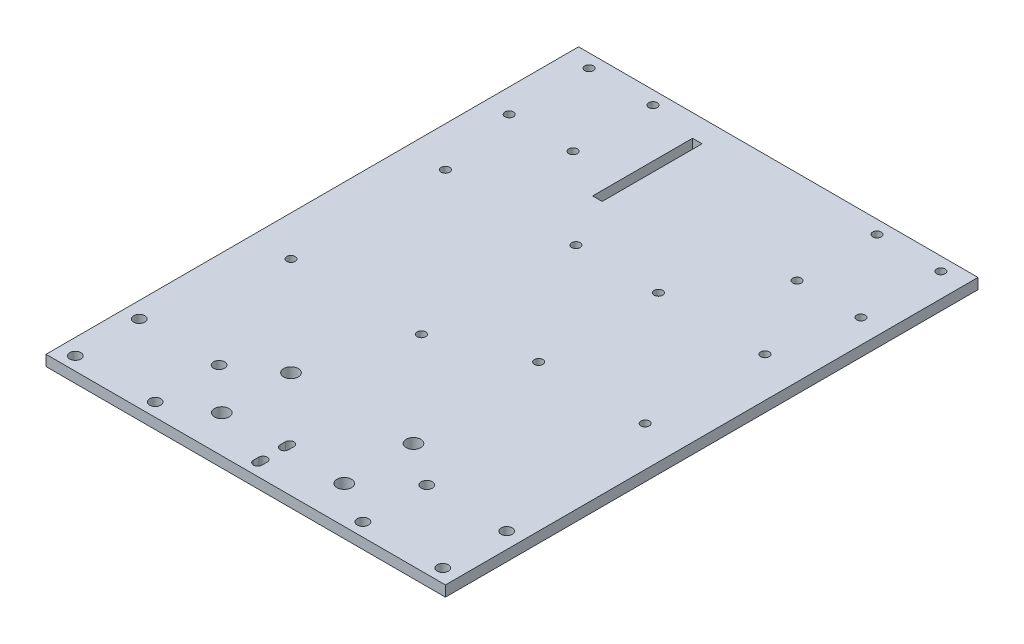
SolidWorks part; units mm, degrees
ref_plane "前视基准面" through (0, 0, 0) normal (0, 0, 1) x (1, 0, 0)
ref_plane "上视基准面" through (0, 0, 0) normal (0, 1, 0) x (1, 0, 0)
ref_plane "右视基准面" through (0, 0, 0) normal (1, 0, 0) x (0, 0, -1)
sketch "草图1" plane through (0, 0, 0) normal (0, 1, 0) x (1, 0, 0)
  line L0 (-75, 70) -> (75, 70)
  line L1 (75, -130) -> (-75, -130)
  line L2 (75, -130) -> (75, 70)
  line L4 (-75, -130) -> (-75, 70)
  point P0 (0, 0)
  dimension "D1" = 150
  dimension "D2" = 200
extrude "凸台-拉伸1" add sketch "草图1" along normal blind 4
sketch "草图2" plane through (0, 4, 0) normal (0, 1, 0) x (1, 0, 0)
  line L0 (0, 75) -> (0, -130) construction
  line L1 (-75, 70) -> (-75, -130) construction
  line L2 (-75, -130) -> (75, -130) construction
  line L3 (75, 70) -> (-75, 70) construction
  line L4 (-1.6, -123.5) -> (-1.6, -125.5)
  line L5 (1.6, -123.5) -> (1.6, -125.5)
  line L6 (-1.6, -113.5) -> (-1.6, -115.5)
  line L7 (1.6, -113.5) -> (1.6, -115.5)
  line L8 (-60, 5) -> (-60, -53) construction
  line L9 (-20.2776, 24.1397) -> (-23.8598, 24.1397)
  line L10 (-20.2776, 24.1397) -> (-20.2776, 61.6471)
  line L11 (-20.2776, 61.6471) -> (-23.8598, 61.6471)
  line L12 (-23.8598, 24.1397) -> (-23.8598, 61.6471)
  line L13 (-20.2776, 24.1397) -> (-23.8598, 61.6471) construction
  line L14 (-20.2776, 61.6471) -> (-23.8598, 24.1397) construction
  line L15 (-60, -53) -> (-11, -53) construction
  line L16 (-11, -53) -> (-11, 5) construction
  line L17 (-11, 5) -> (-60, 5) construction
  line L18 (20, 5) -> (20, -40) construction
  line L19 (20, -40) -> (60, -40) construction
  line L20 (60, -40) -> (60, 5) construction
  line L21 (60, 5) -> (20, 5) construction
  line L22 (75, -130) -> (75, 70) construction
  circle A1 centre (-66.0523, 65) radius 1.6
  circle A2 centre (-66.0523, 35) radius 1.6
  circle A3 centre (-42.0523, 65) radius 1.6
  circle A4 centre (-42.0523, 35) radius 1.6
  circle A5 centre (42.0523, 35) radius 1.6
  circle A6 centre (66.0523, 35) radius 1.6
  circle A7 centre (66.0523, 65) radius 1.6
  circle A8 centre (42.0523, 65) radius 1.6
  circle A12 centre (-23, -90) radius 2.75
  circle A13 centre (-23, -116) radius 2.75
  circle A14 centre (-69, -101) radius 2.1
  circle A15 centre (-69, -125) radius 2.1
  circle A16 centre (69, -125) radius 2.1
  circle A17 centre (69, -101) radius 2.1
  circle A18 centre (23, -116) radius 2.75
  circle A19 centre (23, -90) radius 2.75
  circle A20 centre (-39, -125) radius 2.1
  circle A21 centre (-39, -101) radius 2.1
  circle A22 centre (39, -125) radius 2.1
  circle A23 centre (39, -101) radius 2.1
  arc A26 (1.6, -123.5) -> (-1.6, -123.5) centre (0, -123.5) ccw
  arc A27 (-1.6, -125.5) -> (1.6, -125.5) centre (0, -125.5) ccw
  arc A28 (-1.6, -115.5) -> (1.6, -115.5) centre (0, -115.5) ccw
  arc A30 (1.6, -113.5) -> (-1.6, -113.5) centre (0, -113.5) ccw
  circle A31 centre (-60, 5) radius 1.6
  circle A32 centre (-60, -53) radius 1.6
  circle A33 centre (-11, -53) radius 1.6
  circle A34 centre (-11, 5) radius 1.6
  circle A35 centre (20, 5) radius 1.6
  circle A36 centre (60, 5) radius 1.6
  circle A37 centre (20, -40) radius 1.6
  circle A38 centre (60, -40) radius 1.6
  point P48 (-22.0687, 42.8934)
  dimension "D2" = 24
  dimension "D6" = 6
  dimension "D7" = 4.2
  dimension "D12" = 23
  dimension "D13" = 26
  dimension "D15" = 30
  dimension "D16" = 24
  dimension "D18" = 30
  dimension "D19" = 49
  dimension "D20" = 58
  dimension "D21" = 65
  dimension "D23" = 45
  dimension "D25" = 15
  dimension "D3" = 30
  dimension "D4" = 24
  dimension "D5" = 5
  dimension "D8" = 35
  dimension "D9" = 35
  dimension "D10" = 8.9477
  dimension "D11" = 5
  dimension "D14" = 40
  dimension "D17" = 5
  dimension "D22" = 15
  dimension "D24" = 40
  dimension "D26" = 65
extrude "切除-拉伸1" cut sketch "草图2" against normal through all
